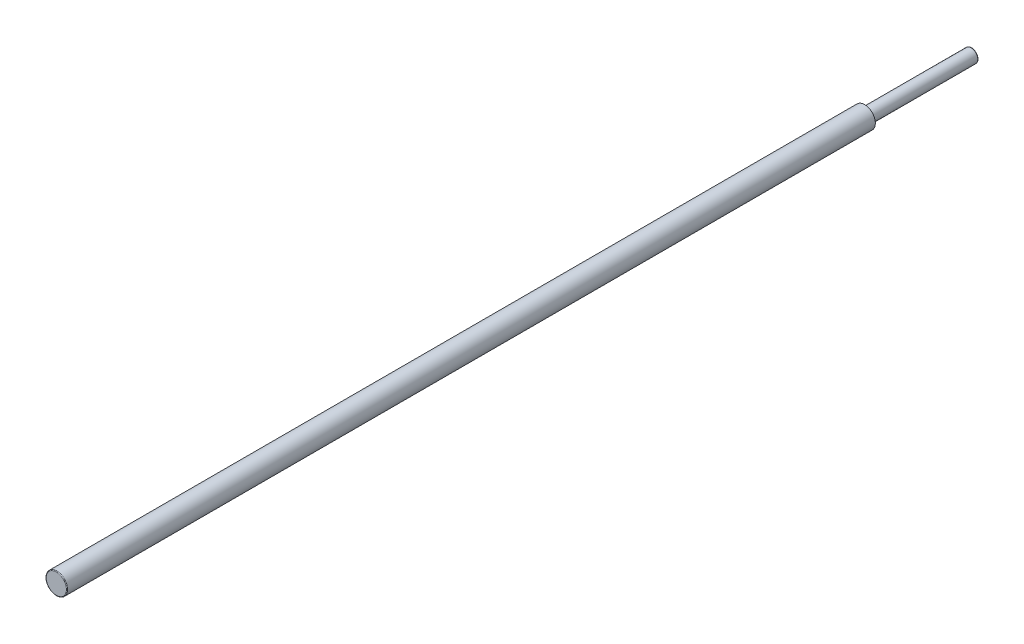
SolidWorks part; units mm, degrees
material "Alloy Steel"
ref_plane "Plane1" through (0, 0, 0) normal (0, 0, 1) x (1, 0, 0)
ref_plane "Plane2" through (0, 0, 0) normal (0, 1, 0) x (1, 0, 0)
ref_plane "Plane3" through (0, 0, 0) normal (1, 0, 0) x (0, 0, -1)
sketch "Sketch1" plane through (0, 0, 0) normal (0, 0, 1) x (1, 0, 0)
  circle A0 centre (0, 0) radius 2.5
  dimension "D1" = 5
extrude "Extrude1" add sketch "Sketch1" along normal blind 40
sketch "Sketch2" plane through (0, 0, 40) normal (0, 0, 1) x (1, 0, 0)
  circle A0 centre (0, 0) radius 4
  dimension "D1" = 8
extrude "Boss-Extrude1" add sketch "Sketch2" along normal blind 302
fillet "Fillet1" radius 0.25 2 edges at (4, 0, 342) (2.5, 0, 0)
